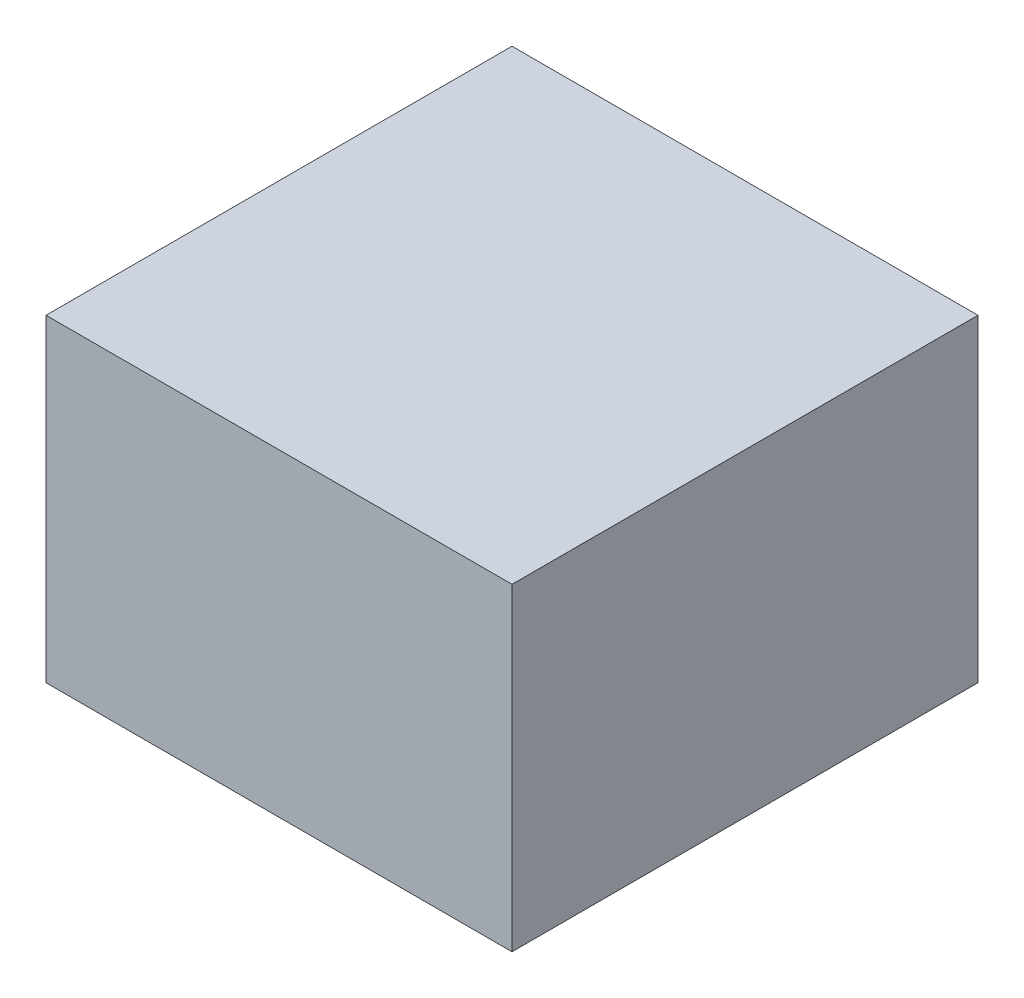
SolidWorks part; units mm, degrees
ref_plane "Front Plane" through (0, 0, 0) normal (0, 0, 1) x (1, 0, 0)
ref_plane "Top Plane" through (0, 0, 0) normal (0, 1, 0) x (1, 0, 0)
ref_plane "Right Plane" through (0, 0, 0) normal (1, 0, 0) x (0, 0, -1)
sketch "Sketch1" plane through (0, 0, 0) normal (0, 1, 0) x (1, 0, 0)
  line L1 (-32.8, 32.8) -> (32.8, 32.8)
  line L2 (-32.8, 32.8) -> (-32.8, -32.8)
  line L3 (-32.8, -32.8) -> (32.8, -32.8)
  line L4 (32.8, 32.8) -> (32.8, -32.8)
  dimension "D1" = 65.6
  dimension "D2" = 65.6
  dimension "D3" = 32.8
  dimension "D4" = 32.8
extrude "Boss-Extrude1" add sketch "Sketch1" along normal mid plane 44.8
